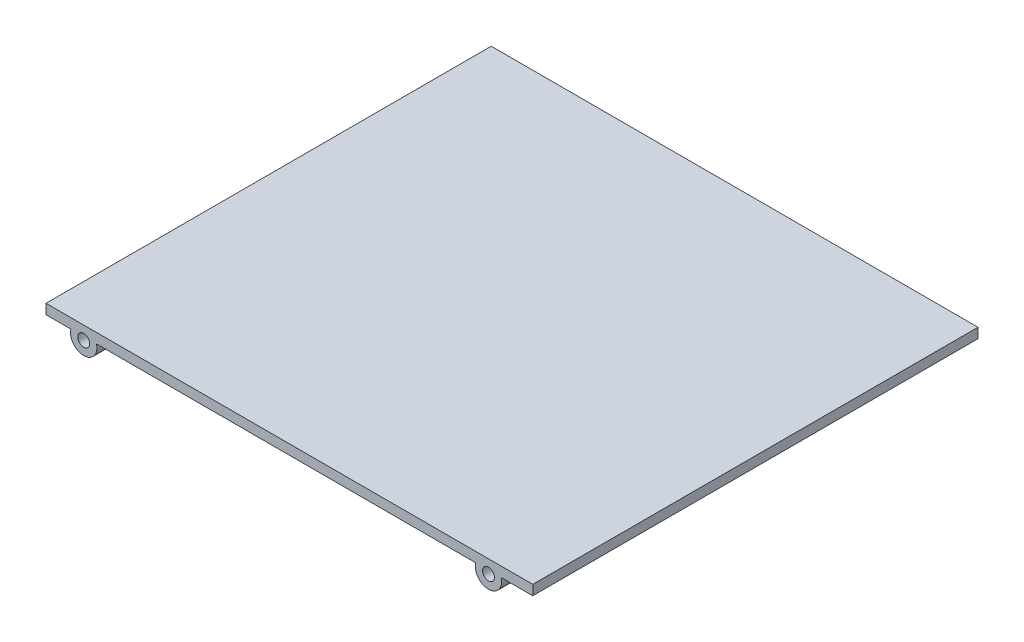
SolidWorks part; units mm, degrees
ref_plane "Front Plane" through (0, 0, 0) normal (0, 0, 1) x (1, 0, 0)
ref_plane "Top Plane" through (0, 0, 0) normal (0, 1, 0) x (1, 0, 0)
ref_plane "Right Plane" through (0, 0, 0) normal (1, 0, 0) x (0, 0, -1)
sketch "Sketch1" plane through (0, 0, 0) normal (0, 0, 1) x (1, 0, 0)
  line L0 (-215.7905, 18.1325) -> (-289.4571, 18.1325)
  line L2 (-289.4571, 19.6325) -> (-289.4571, -0.8675) construction
  line L3 (-289.4571, 18.1325) -> (-289.4571, 19.6325)
  line L4 (-289.4571, 19.6325) -> (-215.7905, 19.6325)
  line L5 (-215.7905, 19.6325) -> (-215.7905, 18.1325)
  line L8 (-215.5905, 19.6325) -> (-215.5905, -20.3675) construction
  dimension "D1" = 1.5
  dimension "D2" = 0.2
extrude "Boss-Extrude1" add sketch "Sketch1" along normal up to surface (67.38 mm away)
sketch "Sketch2" plane through (0, 0, 0) normal (0, 0, -1) x (-1, 0, 0)
  circle A0 centre (283.7505, 17.6325) radius 2
  circle A1 centre (222.4916, 17.6325) radius 2
extrude "Boss-Extrude2" add sketch "Sketch2" against normal blind 8
sketch "Sketch3" plane through (0, 0, 0) normal (0, 0, -1) x (-1, 0, 0)
  circle A0 centre (222.4916, 17.6325) radius 0.9
  circle A1 centre (283.7505, 17.6325) radius 0.9
  dimension "D1" = 1.8
extrude "Cut-Extrude1" cut sketch "Sketch3" against normal blind 8
sketch "Sketch4" plane through (0, 0, 67.38) normal (0, 0, 1) x (1, 0, 0)
  circle A0 centre (-222.4916, 17.6325) radius 2
  circle A1 centre (-283.7505, 17.6325) radius 2
extrude "Boss-Extrude3" add sketch "Sketch4" against normal blind 8
sketch "Sketch5" plane through (0, 0, 67.38) normal (0, 0, 1) x (1, 0, 0)
  circle A0 centre (-283.7505, 17.6325) radius 0.9
  circle A1 centre (-222.4916, 17.6325) radius 0.9
extrude "Cut-Extrude2" cut sketch "Sketch5" against normal blind 8
